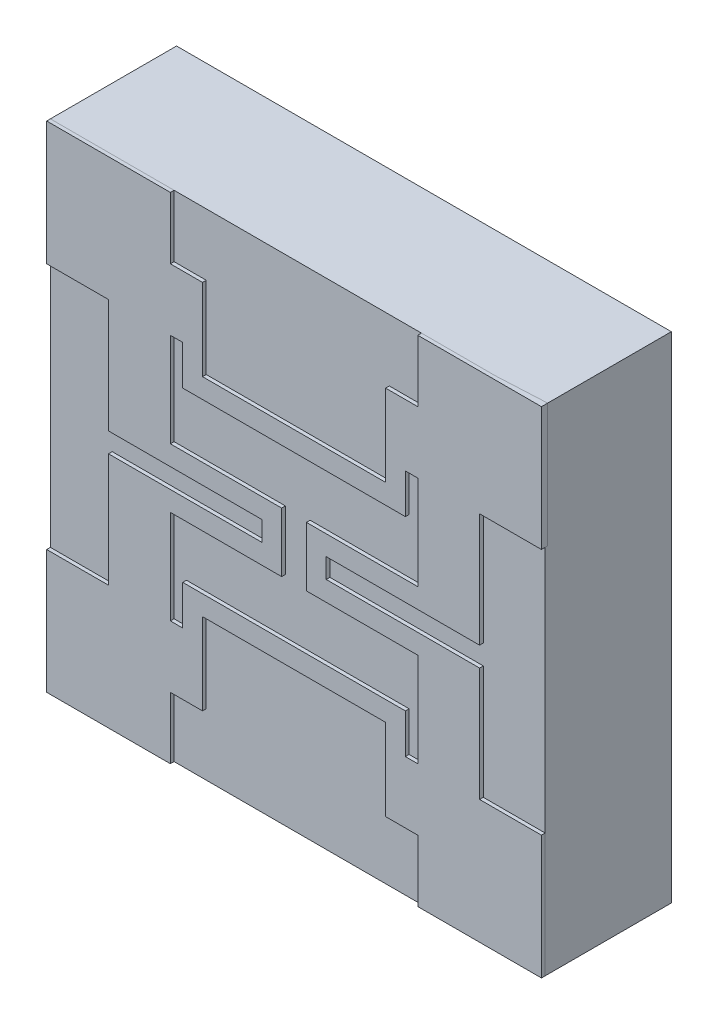
SolidWorks part; units mm, degrees
ref_plane "Front Plane" through (0, 0, 0) normal (0, 0, 1) x (1, 0, 0)
ref_plane "Top Plane" through (0, 0, 0) normal (0, 1, 0) x (1, 0, 0)
ref_plane "Right Plane" through (0, 0, 0) normal (1, 0, 0) x (0, 0, -1)
sketch "top membrane" plane through (0, 0, 0) normal (0, 0, 1) x (1, 0, 0)
  line L1 (-0.45, 0.5) -> (0.45, 0.5)
  line L2 (-0.45, 0.5) -> (-0.45, -0.5)
  line L3 (-0.45, -0.5) -> (0.45, -0.5)
  line L4 (0.45, 0.5) -> (0.45, -0.5)
  line L5 (-0.45, 0.5) -> (0.45, -0.5) construction
  line L6 (-0.45, -0.5) -> (0.45, 0.5) construction
  line L41 (-0.45, 0.5) -> (0.45, -0.5) construction
  line L43 (-0.45, -0.5) -> (0.45, 0.5) construction
  point P3 (0, 0)
  point P48 (0, 0)
sketch "wafer" plane through (0, 0, 0) normal (0, 0, 1) x (1, 0, 0)
  line L16 (-1, 1) -> (1, 1)
  line L36 (-1, -1) -> (1, -1)
  line L39 (-1, 1) -> (-1, -1)
  line L40 (1, 1) -> (1, -1)
  line L41 (-1, 1) -> (1, -1) construction
  line L43 (-1, -1) -> (1, 1) construction
extrude "Boss-Extrude3" add sketch "wafer" against normal blind 0.5
sketch "SiN Layer" plane through (0, 0, 0) normal (0, 0, 1) x (1, 0, 0)
  line L16 (-1, 1) -> (1, 1)
  line L36 (-1, -1) -> (1, -1)
  line L39 (-1, 1) -> (-1, -1)
  line L40 (1, 1) -> (1, -1)
  line L41 (-1, 1) -> (1, -1) construction
  line L43 (-1, -1) -> (1, 1) construction
extrude "Boss-Extrude4" add sketch "SiN Layer" along normal blind 0.01
ref_plane "SiN Plane" through (0, 0, 0.01) normal (0, 0, 1) x (1, 0, 0)
sketch "circuit" plane through (0, 0, 0) normal (0, 0, 1) x (1, 0, 0)
  line L0 (-1, 1) -> (-0.5, 1)
  line L1 (-0.5, 1) -> (-0.5, 0.75)
  line L2 (-0.5, 0.75) -> (-0.37, 0.75)
  line L3 (-0.37, 0.75) -> (-0.37, 0.42)
  line L4 (-0.45, 0.5) -> (-0.5, 0.5)
  line L5 (-0.5, 0.5) -> (-0.5, 0.12)
  line L7 (-0.75, 0.04) -> (-0.75, 0.5)
  line L8 (-0.75, 0.5) -> (-1, 0.5)
  line L9 (-1, 0.5) -> (-1, 1)
  line L10 (1, 1) -> (0.5, 1)
  line L11 (0.5, 1) -> (0.5, 0.75)
  line L12 (0.5, 0.75) -> (0.37, 0.75)
  line L13 (0.37, 0.75) -> (0.37, 0.42)
  line L14 (0.45, 0.5) -> (0.5, 0.5)
  line L15 (0.5, 0.5) -> (0.5, 0.12)
  line L17 (0.75, 0.04) -> (0.75, 0.5)
  line L18 (0.75, 0.5) -> (1, 0.5)
  line L19 (1, 0.5) -> (1, 1)
  line L20 (1, -1) -> (0.5, -1)
  line L21 (0.5, -1) -> (0.5, -0.75)
  line L22 (0.5, -0.75) -> (0.37, -0.75)
  line L23 (0.37, -0.75) -> (0.37, -0.42)
  line L24 (0.45, -0.5) -> (0.5, -0.5)
  line L25 (0.5, -0.5) -> (0.5, -0.12)
  line L27 (0.75, -0.04) -> (0.75, -0.5)
  line L28 (0.75, -0.5) -> (1, -0.5)
  line L29 (1, -0.5) -> (1, -1)
  line L30 (-1, -1) -> (-0.5, -1)
  line L31 (-0.5, -1) -> (-0.5, -0.75)
  line L32 (-0.5, -0.75) -> (-0.37, -0.75)
  line L33 (-0.37, -0.75) -> (-0.37, -0.42)
  line L34 (-0.45, -0.5) -> (-0.5, -0.5)
  line L35 (-0.5, -0.5) -> (-0.5, -0.12)
  line L37 (-0.75, -0.04) -> (-0.75, -0.5)
  line L38 (-0.75, -0.5) -> (-1, -0.5)
  line L39 (-1, -0.5) -> (-1, -1)
  line L42 (0.37, 0.42) -> (-0.37, 0.42)
  line L45 (-0.45, 0.5) -> (-0.45, 0.34)
  line L46 (-0.45, 0.34) -> (0.45, 0.34)
  line L47 (0.45, 0.34) -> (0.45, 0.5)
  line L49 (0.5, 0.12) -> (0.05, 0.12)
  line L50 (0.05, 0.12) -> (0.05, -0.12)
  line L51 (0.05, -0.12) -> (0.5, -0.12)
  line L53 (0.75, -0.04) -> (0.13, -0.04)
  line L54 (0.13, -0.04) -> (0.13, 0.04)
  line L55 (0.13, 0.04) -> (0.75, 0.04)
  line L57 (-0.75, 0.04) -> (-0.13, 0.04)
  line L58 (-0.13, 0.04) -> (-0.13, -0.04)
  line L59 (-0.13, -0.04) -> (-0.75, -0.04)
  line L61 (-0.5, -0.12) -> (-0.05, -0.12)
  line L62 (-0.05, -0.12) -> (-0.05, 0.12)
  line L63 (-0.05, 0.12) -> (-0.5, 0.12)
  line L66 (-0.37, -0.42) -> (0.37, -0.42)
  line L69 (0.45, -0.5) -> (0.45, -0.34)
  line L70 (0.45, -0.34) -> (-0.45, -0.34)
  line L71 (-0.45, -0.34) -> (-0.45, -0.5)
  point P48 (0, 0)
extrude "Boss-Extrude5" add sketch "circuit" along normal blind 0.025 separate body
ref_plane "Wafer bottom plane" through (0, 0, -0.5) normal (0, 0, 1) x (1, 0, 0)
sketch "bottom" plane through (0, 0, -0.5) normal (0, 0, 1) x (1, 0, 0)
  line L72 (-0.9808, -0.9808) -> (0.9808, -0.9808)
  line L73 (0.9808, -0.9808) -> (0.9808, 0.9808)
  line L74 (0.9808, 0.9808) -> (-0.9808, 0.9808)
  line L75 (-0.9808, 0.9808) -> (-0.9808, -0.9808)
loft "Cut-Loft8" cut profiles "top membrane", "bottom"
